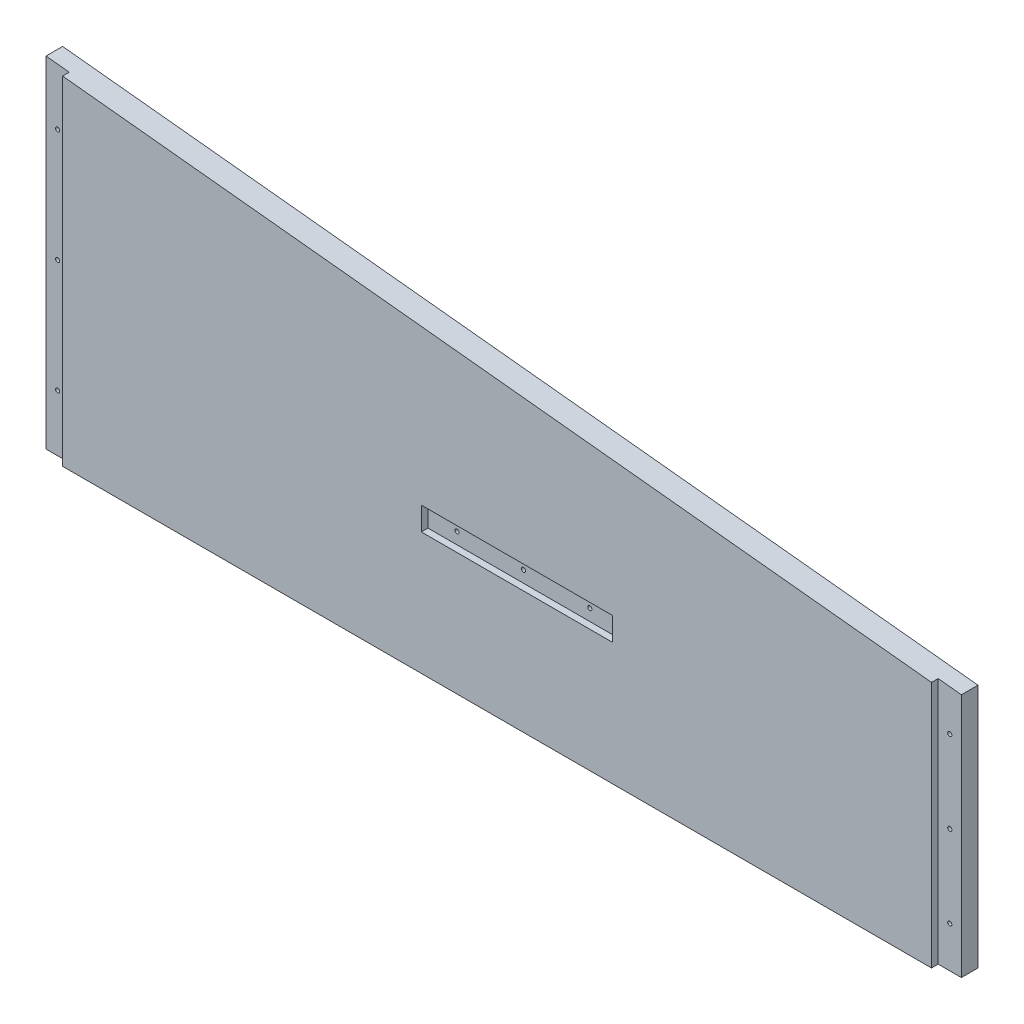
SolidWorks part; units mm, degrees
material "Pine"
ref_plane "Front Plane" through (0, 0, 0) normal (0, 0, 1) x (1, 0, 0)
ref_plane "Top Plane" through (0, 0, 0) normal (0, 1, 0) x (1, 0, 0)
ref_plane "Right Plane" through (0, 0, 0) normal (1, 0, 0) x (0, 0, -1)
sketch "Sketch1" plane through (0, 0, 0) normal (0, 0, 1) x (1, 0, 0)
  line L0 (-163.9887, -5335.905) -> (-163.9887, -5432.425)
  line L1 (-102.87, -5350.891) -> (-33.02, -5350.891)
  line L2 (-111.8235, -5341.9375) -> (-111.8235, -5334)
  line L3 (-24.0665, -5341.9375) -> (-24.0665, -5334)
  line L4 (-298.9262, -5332.73) -> (-167.1637, -5332.73)
  line L5 (-167.1637, -5435.6) -> (-298.9262, -5435.6)
  line L6 (-302.1012, -5432.425) -> (-302.1012, -5335.905)
  line L7 (-107.6325, -5329.809) -> (-28.2575, -5329.809)
  line L8 (174.9425, -5308.6) -> (174.9425, -5581.65)
  line L9 (449.2625, -5413.1661) -> (449.2625, -5421.9659)
  line L10 (595.3125, -5421.9659) -> (595.3125, -5413.1661)
  line L11 (839.47, -5509.5521) -> (839.47, -5307.6729)
  line L12 (839.47, -5307.6729) -> (863.6, -5307.6729)
  line L13 (839.47, -5509.5521) -> (863.6, -5509.5521)
  line L14 (863.6, -5509.5521) -> (863.6, -5307.6729)
  line L15 (-354.2665, -5341.9375) -> (-354.2665, -5334)
  line L16 (-100.8856, -5889.625) -> (-50.0856, -5889.625)
  line L17 (-104.0606, -5969) -> (-104.0606, -5892.8)
  line L18 (-46.9106, -5892.8) -> (-46.9106, -5969)
  line L19 (-50.0856, -5972.175) -> (-100.8856, -5972.175)
  line L20 (-100.8856, -5848.35) -> (-50.0856, -5848.35)
  line L21 (857.25, -5502.275) -> (157.1625, -5575.3)
  line L22 (857.25, -5314.95) -> (857.25, -5502.275)
  line L23 (157.1625, -5314.95) -> (157.1625, -5575.3)
  line L24 (857.25, -5314.95) -> (157.1625, -5314.95)
  line L25 (150.8125, -5308.6) -> (174.9425, -5308.6)
  line L26 (174.9425, -5581.65) -> (150.8125, -5581.65)
  line L27 (137.16, -5314.95) -> (137.16, -5502.275)
  line L28 (150.8125, -5581.65) -> (150.8125, -5308.6)
  line L29 (590.8224, -5408.676) -> (453.7526, -5408.676)
  line L30 (453.7526, -5426.456) -> (590.8224, -5426.456)
  line L31 (137.16, -6013.45) -> (137.16, -5867.4)
  line L32 (150.8125, -5746.75) -> (150.8125, -6019.8)
  line L33 (143.51, -5639.9938) -> (143.51, -5654.294)
  line L34 (590.8224, -5919.724) -> (453.7526, -5919.724)
  line L35 (453.7526, -5901.944) -> (590.8224, -5901.944)
  line L36 (449.2625, -5915.2339) -> (449.2625, -5906.4341)
  line L37 (174.9425, -6019.8) -> (174.9425, -5746.75)
  line L38 (595.3125, -5906.4341) -> (595.3125, -5915.2339)
  line L39 (839.47, -5818.8479) -> (839.47, -6020.7271)
  line L40 (839.47, -5818.8479) -> (863.6, -5818.8479)
  line L41 (863.6, -5818.8479) -> (863.6, -6020.7271)
  line L42 (839.47, -6020.7271) -> (863.6, -6020.7271)
  line L43 (-155.8782, -5867.4) -> (-603.25, -5867.4)
  line L44 (-433.07, -5350.891) -> (-363.22, -5350.891)
  line L45 (-437.8325, -5329.809) -> (-358.4575, -5329.809)
  line L46 (889, -6045.2) -> (-635, -6045.2)
  line L47 (-635, -5283.2) -> (889, -5283.2)
  line L48 (-635, -6045.2) -> (-635, -5283.2)
  line L49 (889, -5283.2) -> (889, -6045.2)
  line L50 (137.16, -5502.275) -> (-603.25, -5502.275)
  line L51 (-603.25, -5314.95) -> (137.16, -5314.95)
  line L52 (143.51, -5654.294) -> (-609.6, -5654.294)
  line L53 (-609.6, -5639.9938) -> (143.51, -5639.9938)
  line L54 (137.16, -5536.0062) -> (-603.25, -5536.0062)
  line L55 (-603.25, -5794.375) -> (137.16, -5794.375)
  line L56 (-603.25, -6013.45) -> (137.16, -6013.45)
  line L57 (-603.25, -5536.0062) -> (-603.25, -5794.375)
  line L58 (137.16, -5794.375) -> (137.16, -5536.0062)
  line L59 (-609.6, -5654.294) -> (-609.6, -5639.9938)
  line L60 (-603.25, -5867.4) -> (-603.25, -6013.45)
  line L61 (-603.25, -5314.95) -> (-603.25, -5502.275)
  line L62 (-442.0235, -5341.9375) -> (-442.0235, -5334)
  line L63 (857.25, -5826.125) -> (157.1625, -5753.1)
  line L64 (857.25, -6013.45) -> (857.25, -5826.125)
  line L65 (157.1625, -6013.45) -> (157.1625, -5753.1)
  line L66 (857.25, -6013.45) -> (157.1625, -6013.45)
  line L67 (174.9425, -5746.75) -> (150.8125, -5746.75)
  line L68 (150.8125, -6019.8) -> (174.9425, -6019.8)
  line L69 (137.16, -5867.4) -> (4.907, -5867.4)
  circle A0 centre (-36.195, -5484.0124) radius 1.5875
  arc A1 (-298.9262, -5332.73) -> (-302.1012, -5335.905) centre (-298.9262, -5335.905) ccw
  arc A2 (-302.1012, -5432.425) -> (-298.9262, -5435.6) centre (-298.9262, -5432.425) ccw
  arc A3 (-163.9887, -5335.905) -> (-167.1637, -5332.73) centre (-167.1637, -5335.905) ccw
  arc A4 (-167.1637, -5435.6) -> (-163.9887, -5432.425) centre (-167.1637, -5432.425) ccw
  arc A5 (-111.8235, -5341.9375) -> (-102.87, -5350.891) centre (-102.87, -5341.9375) ccw
  arc A6 (-107.6325, -5329.809) -> (-111.8235, -5334) centre (-107.6325, -5334) ccw
  circle A7 centre (166.0525, -5444.6613) radius 1.5875
  circle A8 centre (166.0525, -5358.1871) radius 1.5875
  circle A9 centre (471.4875, -5417.566) radius 1.5875
  arc A10 (453.7526, -5408.676) -> (449.2625, -5413.1661) centre (451.5076, -5410.9211) ccw
  arc A11 (449.2625, -5421.9659) -> (453.7526, -5426.456) centre (451.5076, -5424.2109) ccw
  circle A12 centre (522.2875, -5417.566) radius 1.5875
  circle A13 centre (573.0875, -5417.566) radius 1.5875
  arc A14 (590.8224, -5426.456) -> (595.3125, -5421.9659) centre (593.0674, -5424.2109) ccw
  arc A15 (595.3125, -5413.1661) -> (590.8224, -5408.676) centre (593.0674, -5410.9211) ccw
  circle A16 centre (848.36, -5471.8269) radius 1.5875
  circle A17 centre (848.36, -5409.0762) radius 1.5875
  circle A18 centre (848.36, -5346.3254) radius 1.5875
  arc A19 (-363.22, -5350.891) -> (-354.2665, -5341.9375) centre (-363.22, -5341.9375) ccw
  arc A20 (-354.2665, -5334) -> (-358.4575, -5329.809) centre (-358.4575, -5334) ccw
  arc A21 (-24.0665, -5334) -> (-28.2575, -5329.809) centre (-28.2575, -5334) ccw
  arc A22 (-33.02, -5350.891) -> (-24.0665, -5341.9375) centre (-33.02, -5341.9375) ccw
  circle A23 centre (-86.995, -5484.0124) radius 1.5875
  circle A24 centre (-333.4544, -5894.07) radius 2.54
  circle A25 centre (-333.4544, -5994.4) radius 2.54
  arc A26 (-104.0606, -5969) -> (-100.8856, -5972.175) centre (-100.8856, -5969) ccw
  arc A27 (-50.0856, -5972.175) -> (-46.9106, -5969) centre (-50.0856, -5969) ccw
  arc A28 (-100.8856, -5848.35) -> (-128.3819, -5857.875) centre (-100.8856, -5892.8) ccw
  arc A29 (-155.8782, -5867.4) -> (-128.3819, -5857.875) centre (-155.8782, -5822.95) ccw
  arc A30 (-22.5893, -5857.875) -> (-50.0856, -5848.35) centre (-50.0856, -5892.8) ccw
  circle A31 centre (-132.6356, -5894.07) radius 2.54
  circle A32 centre (-132.6356, -5994.4) radius 2.54
  arc A33 (-46.9106, -5892.8) -> (-50.0856, -5889.625) centre (-50.0856, -5892.8) ccw
  arc A34 (-100.8856, -5889.625) -> (-104.0606, -5892.8) centre (-100.8856, -5892.8) ccw
  arc A35 (-22.5893, -5857.875) -> (4.907, -5867.4) centre (4.907, -5822.95) ccw
  circle A36 centre (166.0525, -5531.1356) radius 1.5875
  arc A37 (449.2625, -5915.2339) -> (453.7526, -5919.724) centre (451.5076, -5917.4789) ccw
  arc A38 (453.7526, -5901.944) -> (449.2625, -5906.4341) centre (451.5076, -5904.1891) ccw
  circle A39 centre (166.0525, -5797.2644) radius 1.5875
  circle A40 centre (166.0525, -5883.7387) radius 1.5875
  circle A41 centre (166.0525, -5970.2129) radius 1.5875
  circle A42 centre (471.4875, -5910.834) radius 1.5875
  circle A43 centre (522.2875, -5910.834) radius 1.5875
  circle A44 centre (573.0875, -5910.834) radius 1.5875
  arc A45 (595.3125, -5906.4341) -> (590.8224, -5901.944) centre (593.0674, -5904.1891) ccw
  arc A46 (590.8224, -5919.724) -> (595.3125, -5915.2339) centre (593.0674, -5917.4789) ccw
  circle A47 centre (848.36, -5919.3238) radius 1.5875
  circle A48 centre (848.36, -5982.0746) radius 1.5875
  circle A49 centre (848.36, -5856.5731) radius 1.5875
  arc A50 (-437.8325, -5329.809) -> (-442.0235, -5334) centre (-437.8325, -5334) ccw
  circle A51 centre (-429.895, -5484.0124) radius 1.5875
  arc A52 (-442.0235, -5341.9375) -> (-433.07, -5350.891) centre (-433.07, -5341.9375) ccw
  circle A53 centre (-379.095, -5484.0124) radius 1.5875
sketch "Sketch7" plane through (0, 0, 0) normal (0, 0, 1) x (1, 0, 0)
  line L0 (157.1625, -6013.45) -> (857.25, -6013.45)
  line L1 (857.25, -6013.45) -> (857.25, -5826.125)
  line L2 (857.25, -5826.125) -> (157.1625, -5753.1)
  line L3 (157.1625, -5753.1) -> (157.1625, -6013.45)
extrude "Extrude3" add sketch "Sketch7" against normal blind 17.78
sketch "Sketch8" plane through (0, 0, 0) normal (0, 0, 1) x (1, 0, 0)
  circle A0 centre (166.0525, -5970.2129) radius 1.5875
  circle A1 centre (166.0525, -5883.7387) radius 1.5875
  circle A2 centre (166.0525, -5797.2644) radius 1.5875
  circle A3 centre (848.36, -5982.0746) radius 1.5875
  circle A4 centre (848.36, -5919.3238) radius 1.5875
  circle A5 centre (848.36, -5856.5731) radius 1.5875
  circle A6 centre (471.4875, -5910.834) radius 1.5875
  circle A7 centre (522.2875, -5910.834) radius 1.5875
  circle A8 centre (573.0875, -5910.834) radius 1.5875
extrude "Cut-Extrude4" cut sketch "Sketch8" against normal up to surface (17.78 mm away) up to face at (507.2062, -5901.5312, -17.78)
sketch "Sketch9" plane through (0, 0, 0) normal (0, 0, 1) x (1, 0, 0)
  line L0 (157.1625, -5753.1) -> (157.1625, -6013.45)
  line L1 (157.1625, -6013.45) -> (174.9425, -6013.45)
  line L2 (174.9425, -6019.8) -> (174.9425, -5746.75) construction
  line L3 (857.25, -6013.45) -> (157.1625, -6013.45) construction
  line L4 (174.9425, -6013.45) -> (174.9425, -5753.1)
  line L5 (174.9425, -5753.1) -> (157.1625, -5753.1)
  line L6 (857.25, -6013.45) -> (839.47, -6013.45)
  line L7 (839.47, -5818.8479) -> (839.47, -6020.7271) construction
  line L8 (839.47, -6013.45) -> (839.47, -5824.2704)
  line L9 (857.25, -5826.125) -> (157.1625, -5753.1) construction
  line L10 (839.47, -5824.2704) -> (857.25, -5824.2704)
  line L11 (857.25, -5824.2704) -> (857.25, -6013.45)
  line L12 (449.2625, -5919.724) -> (595.3125, -5919.724)
  line L13 (449.2625, -5901.944) -> (595.3125, -5901.944)
  line L14 (449.2625, -5901.944) -> (449.2625, -5919.724)
  line L15 (595.3125, -5901.944) -> (595.3125, -5919.724)
extrude "Cut-Extrude5" cut sketch "Sketch9" against normal blind 5.08
